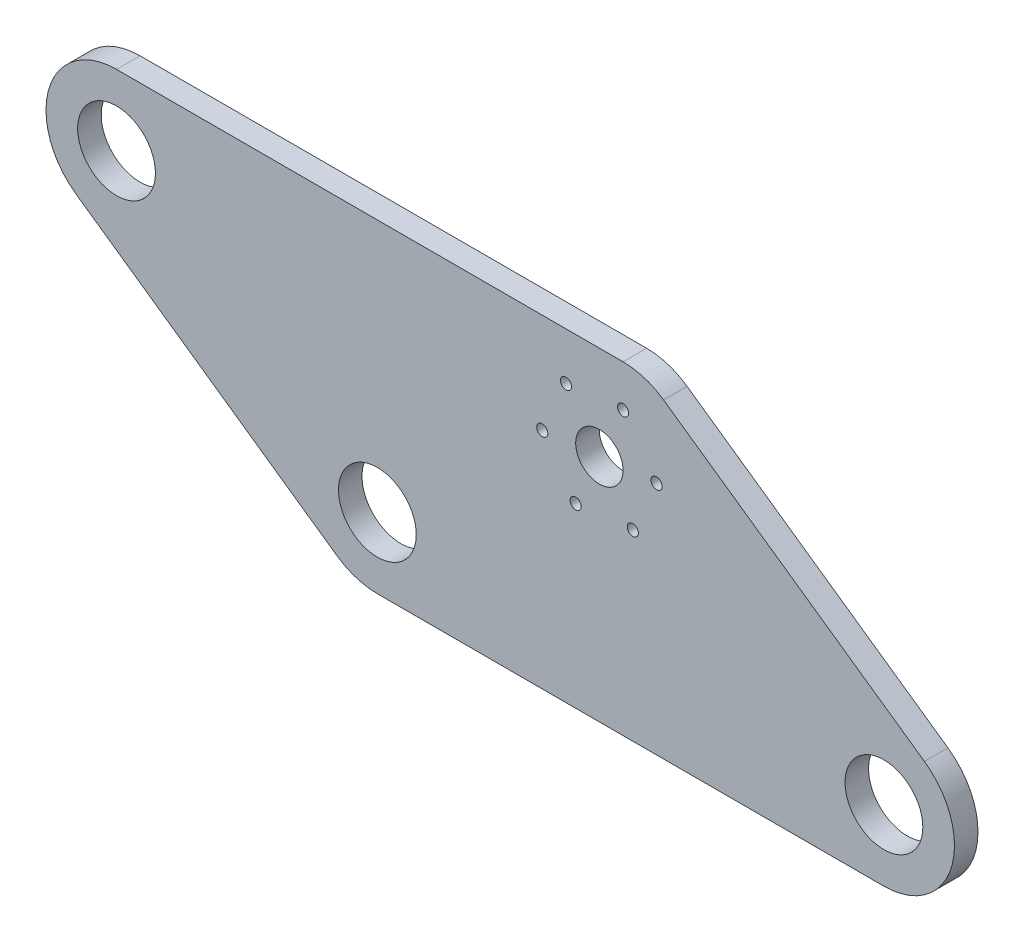
SolidWorks part; units mm, degrees
ref_plane "Front Plane" through (0, 0, 0) normal (0, 0, 1) x (1, 0, 0)
ref_plane "Top Plane" through (0, 0, 0) normal (0, 1, 0) x (1, 0, 0)
ref_plane "Right Plane" through (0, 0, 0) normal (1, 0, 0) x (0, 0, -1)
sketch "Sketch3" plane through (0, 0, 0) normal (0, 0, 1) x (1, 0, 0)
  line L0 (-152.4, 25.4) -> (50.8, 25.4)
  line L1 (50.8, 25.4) -> (175.6388, -62.013)
  line L2 (175.6388, -62.013) -> (-27.5612, -62.013)
  line L3 (-27.5612, -62.013) -> (-152.4, 25.4)
  point P2 (-82.5797, 37.0352)
  point P8 (26.9206, 14.9688)
  dimension "D1" = 35
  dimension "D2" = 203.2
  dimension "D3" = 50.8
  dimension "D4" = 25.4
  dimension "D5" = 152.4
extrude "Boss-Extrude1" add sketch "Sketch3" along normal blind 6.35
fillet "Fillet1" radius 19.05 4 edges at (50.8, 25.4, 3.175) (-27.5612, -62.013, 3.175) (175.6388, -62.013, 3.175) (-152.4, 25.4, 3.175)
sketch "Sketch4" plane through (0, 0, 6.35) normal (0, 0, 1) x (1, 0, 0)
  line L0 (-60.7769, 6.4) -> (76.8744, 6.4) construction
  line L1 (-122.7202, 16.85) -> (97.9806, 16.85) construction
  line L2 (-72.1743, -53.463) -> (175.2876, -53.463) construction
  line L3 (44.7936, -0.6327) -> (44.7936, 26.5757) construction
  circle A0 centre (-91.9811, 6.35) radius 10.5
  circle A1 centre (38.3936, 0) radius 6.4
  circle A2 centre (-21.5548, -42.963) radius 10.5
  circle A3 centre (115.2199, -42.963) radius 10.5
  arc A5 (115.2199, -62.013) -> (126.1465, -27.3582) centre (115.2199, -42.963) ccw construction
  arc A6 (-32.4814, -58.5679) -> (-21.5548, -62.013) centre (-21.5548, -42.963) ccw construction
  circle A7 centre (44.7936, 14.117) radius 1.5
  circle A8 centre (53.8192, 1.5159) radius 1.5
  circle A9 centre (47.4192, -12.6011) radius 1.5
  circle A10 centre (31.9936, -14.117) radius 1.5
  circle A11 centre (22.9679, -1.5159) radius 1.5
  circle A12 centre (29.3679, 12.6011) radius 1.5
  point P11 (38.2683, 0)
  point P29 (0, 0)
  dimension "D1" = 21
  dimension "D2" = 12.8
  dimension "D3" = 21
  dimension "D4" = 21
  dimension "D5" = 3
  dimension "D6" = 15.5
  dimension "D7" = 6
extrude "Cut-Extrude1" cut sketch "Sketch4" against normal through all
